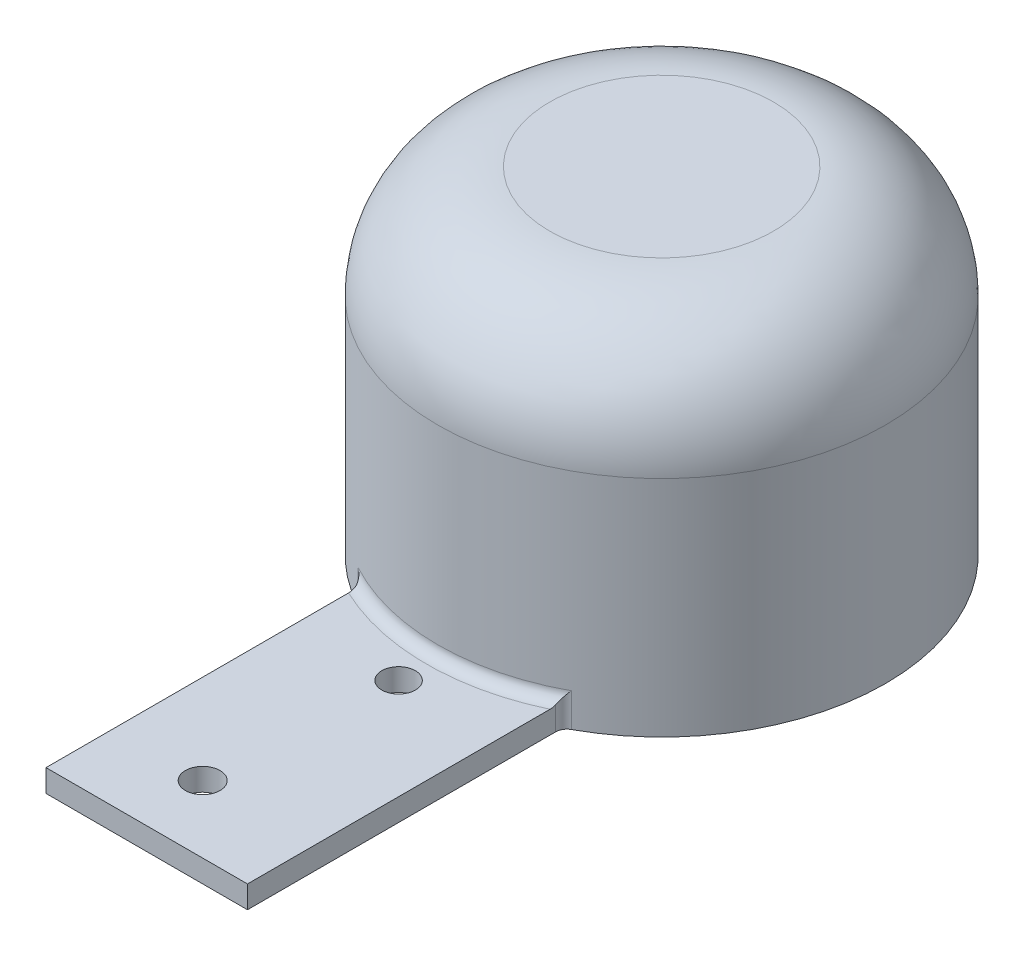
SolidWorks part; units mm, degrees
material "1060 Alloy"
ref_plane "Front Plane" through (0, 0, 0) normal (0, 0, 1) x (1, 0, 0)
ref_plane "Top Plane" through (0, 0, 0) normal (0, 1, 0) x (1, 0, 0)
ref_plane "Right Plane" through (0, 0, 0) normal (1, 0, 0) x (0, 0, -1)
sketch "Sketch1" plane through (0, 0, 0) normal (0, 1, 0) x (1, 0, 0)
  circle A0 centre (0, 0) radius 20
  dimension "D1" = 40
extrude "Boss-Extrude1" add sketch "Sketch1" along normal blind 30
sketch "Sketch2" plane through (0, 0, 0) normal (0, -1, 0) x (1, 0, 0)
  line L0 (-9, 46) -> (-9, 17.8606)
  line L1 (-9, 46) -> (9, 46)
  line L2 (9, 46) -> (9, 17.8606)
  line L3 (0, 0) -> (0, 50000) construction
  circle A0 centre (0, 0) radius 20 construction
  arc A1 (-9, 17.8606) -> (9, 17.8606) centre (0, 0) cw
  point P11 (0, 20)
  point P12 (0, 46)
  dimension "D1" = 18
  dimension "D2" = 26
extrude "Boss-Extrude2" add sketch "Sketch2" against normal blind 2
sketch "Sketch3" plane through (0, 2, 0) normal (0, 1, 0) x (1, 0, 0)
  circle A0 centre (-1, -40) radius 1.55
  circle A1 centre (0, -23.5) radius 1.5
  circle A2 centre (-1, -40) radius 1.55 construction
  circle A3 centre (0, -23.5) radius 1.5 construction
extrude "Cut-Extrude1" cut sketch "Sketch3" against normal up to surface (2 mm away) up to face at (0, 0, 22.4651)
fillet "Fillet1" radius 1 3 edges at (0, 2, 20) (-9, 1, 17.8606) (9, 1, 17.8606)
fillet "Fillet2" radius 10 1 edges at (0, 30, 20)
